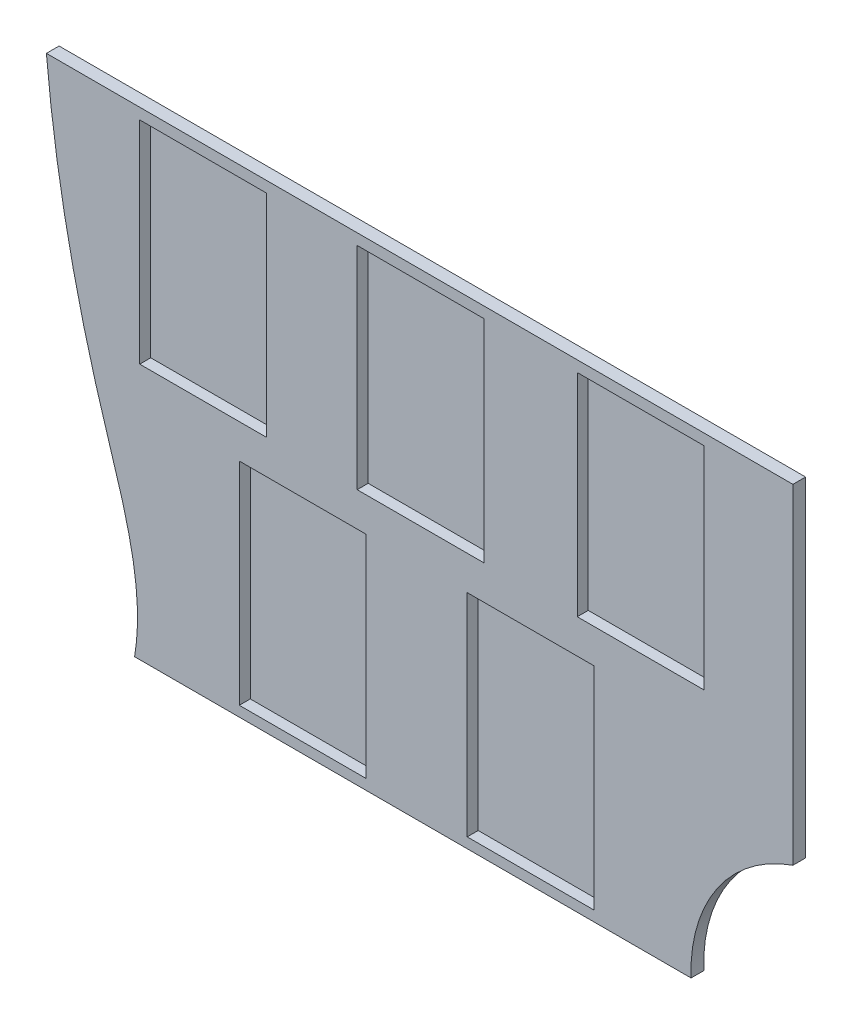
SolidWorks part; units mm, degrees
ref_plane "Front" through (0, 0, 0) normal (0, 0, 1) x (1, 0, 0)
ref_plane "Top" through (0, 0, 0) normal (0, 1, 0) x (1, 0, 0)
ref_plane "Right" through (0, 0, 0) normal (1, 0, 0) x (0, 0, -1)
sketch "Sketch1" plane through (0, 0, 0) normal (0, 0, 1) x (1, 0, 0)
  line L0 (0, 0) -> (65.7673, 0)
  line L1 (77.8041, 17.5546) -> (77.8041, 76.0751)
  line L2 (77.8041, 76.0751) -> (-10.9246, 76.0751)
  line L3 (50.9804, 0) -> (50.9804, 56.55) construction
  arc A0 (65.7673, 0) -> (77.8041, 17.5546) centre (83.6444, 0.646) cw
  spline S0 degree 3 poles (-10.9246, 76.0751) (-11.3352, 65.7011) (-10.1349, 47.6105) (-4.2048, 22.5706) (1.3246, 7.9426) (0, 0) knots 0 0 0 0 0.403328 0.698479 1 1 1 1
  dimension "D2" = 17.8888
  dimension "D7" = 77.3538
  dimension "D1" = 65.7673
  dimension "D3" = 88.7287
  dimension "D4" = 76.0751
  dimension "D5" = 58.5204
  dimension "D6" = 21.2849
extrude "Boss-Extrude1" add sketch "Sketch1" along normal blind 1.5
ref_plane "Plane1" through (0, 0, 11.5) normal (0, 0, 1) x (1, 0, 0)
sketch "Sketch2" plane through (0, 0, 11.5) normal (0, 0, 1) x (1, 0, 0)
  line L0 (41.3742, 0) -> (41.3742, 56.55) construction
  line L1 (0, 0) -> (65.7673, 0) construction
  line L3 (-39.6441, 87.3872) -> (105.1228, 87.3872)
  line L4 (-39.6441, 87.3872) -> (-39.6441, 56.55)
  line L5 (-39.6441, 56.55) -> (105.1228, 56.55)
  line L6 (105.1228, 87.3872) -> (105.1228, 56.55)
  dimension "D1" = 56.55
extrude "Cut-Extrude1" cut sketch "Sketch2" against normal blind 65.5
ref_plane "Plane2" through (0, 0, 1.5) normal (0, 0, 1) x (1, 0, 0)
sketch "Sketch3" plane through (0, 0, 1.5) normal (0, 0, 1) x (1, 0, 0)
  line L1 (0.6047, 55.2507) -> (15.6047, 55.2507)
  line L2 (0.6047, 55.2507) -> (0.6047, 30.2507)
  line L3 (0.6047, 30.2507) -> (15.6047, 30.2507)
  line L4 (15.6047, 55.2507) -> (15.6047, 30.2507)
  line L5 (26.3053, 55.2507) -> (41.3053, 55.2507)
  line L6 (26.3053, 55.2507) -> (26.3053, 30.2507)
  line L7 (26.3053, 30.2507) -> (41.3053, 30.2507)
  line L8 (41.3053, 55.2507) -> (41.3053, 30.2507)
  line L9 (52.3156, 55.2507) -> (67.3156, 55.2507)
  line L10 (52.3156, 55.2507) -> (52.3156, 30.2507)
  line L11 (52.3156, 30.2507) -> (67.3156, 30.2507)
  line L12 (67.3156, 55.2507) -> (67.3156, 30.2507)
  line L13 (12.3713, 26.2176) -> (27.3713, 26.2176)
  line L14 (12.3713, 26.2176) -> (12.3713, 1.2176)
  line L15 (12.3713, 1.2176) -> (27.3713, 1.2176)
  line L16 (27.3713, 26.2176) -> (27.3713, 1.2176)
  line L17 (39.3104, 26.2176) -> (54.3104, 26.2176)
  line L18 (39.3104, 26.2176) -> (39.3104, 1.2176)
  line L19 (39.3104, 1.2176) -> (54.3104, 1.2176)
  line L20 (54.3104, 26.2176) -> (54.3104, 1.2176)
  dimension "D1" = 15
  dimension "D2" = 25
  dimension "D3" = 25
  dimension "D4" = 25
  dimension "D5" = 25
  dimension "D6" = 25
  dimension "D7" = 15
  dimension "D8" = 15
  dimension "D9" = 15
  dimension "D10" = 15
extrude "Cut-Extrude2" cut sketch "Sketch3" against normal blind 1.3
